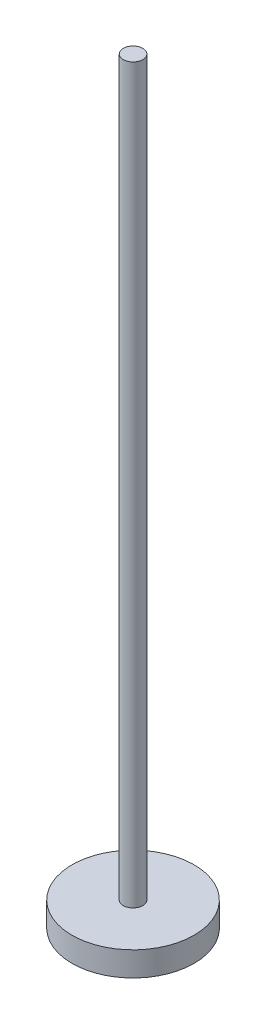
SolidWorks part; units mm, degrees
ref_plane "Front Plane" through (0, 0, 0) normal (0, 0, 1) x (1, 0, 0)
ref_plane "Top Plane" through (0, 0, 0) normal (0, 1, 0) x (1, 0, 0)
ref_plane "Right Plane" through (0, 0, 0) normal (1, 0, 0) x (0, 0, -1)
sketch "Sketch1" plane through (0, 0, 0) normal (0, 0, 1) x (1, 0, 0)
  line L0 (0, -1655.0005) -> (0, 81095.0265) construction
  line L1 (4, 300) -> (4, 0)
  line L2 (4, 0) -> (25, 0)
  line L3 (25, 0) -> (25, -10)
  line L4 (25, -10) -> (0, -10)
  line L5 (4, 300) -> (0, 300)
  line L6 (0, -10) -> (0, 300)
  dimension "D1" = 4
  dimension "D2" = 300
  dimension "D3" = 25
  dimension "D4" = 10
revolve "Revolve1" add sketch "Sketch1" angle 360 about L0
